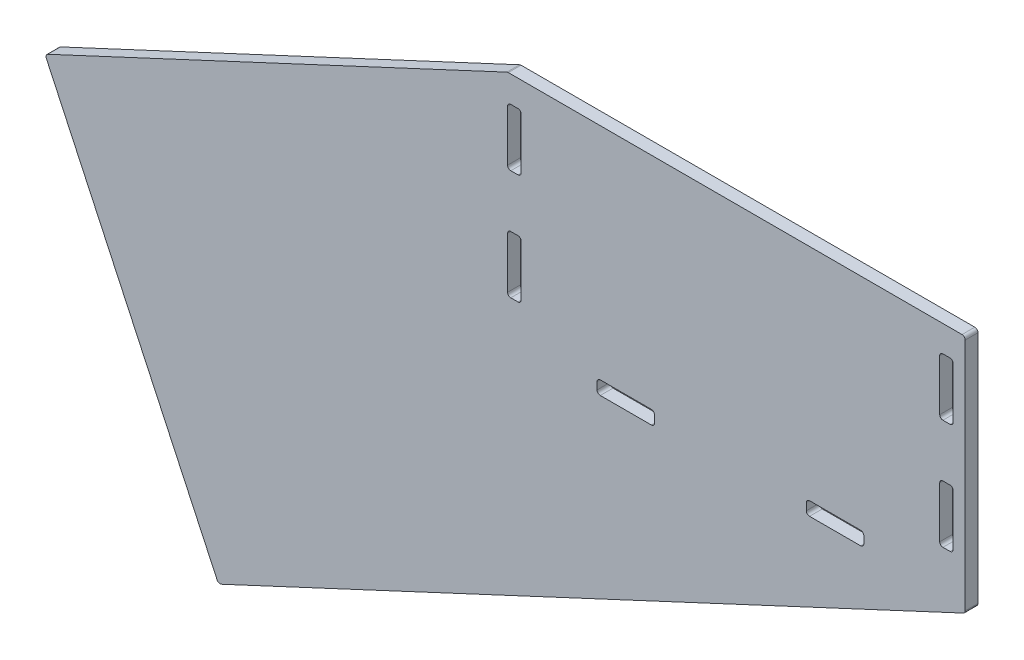
SolidWorks part; units mm, degrees
material "PE High Density"
ref_plane "Front Plane" through (0, 0, 0) normal (0, 0, 1) x (1, 0, 0)
ref_plane "Top Plane" through (0, 0, 0) normal (0, 1, 0) x (1, 0, 0)
ref_plane "Right Plane" through (0, 0, 0) normal (1, 0, 0) x (0, 0, -1)
sketch "Sketch1" plane through (0, 0, 0) normal (0, 0, 1) x (1, 0, 0)
  line L0 (-208.28, 0) -> (208.28, 0)
  line L1 (208.28, 0) -> (208.28, -219.075)
  line L2 (208.28, -219.075) -> (-208.28, -219.075)
  line L3 (-208.28, -219.075) -> (-208.28, 0)
  point P2 (0, 0)
  dimension "D1" = 219.075
  dimension "D2" = 416.56
extrude "Boss-Extrude1" add sketch "Sketch1" along normal mid plane 12.7
sketch "Sketch2" plane through (0, 0, 0) normal (0, 0, 1) x (1, 0, 0)
  line L0 (-221.742, 0) -> (-682.1464, -214.6901)
  line L1 (-682.1464, -214.6901) -> (-509.4341, -585.0727)
  line L2 (-509.4341, -585.0727) -> (233.68, -238.5529)
  line L3 (233.68, -238.5529) -> (233.68, 0)
  line L4 (233.68, 0) -> (208.28, 0)
  line L5 (208.28, 0) -> (208.28, -26.1938)
  line L6 (208.28, -219.075) -> (132.715, -219.075)
  line L7 (-208.28, -219.075) -> (-208.28, -192.8813)
  line L8 (208.28, 0) -> (-208.28, 0) construction
  line L9 (208.28, -219.075) -> (208.28, -244.475) construction
  line L10 (208.28, -83.3438) -> (208.28, -135.7312)
  line L11 (208.28, -26.1938) -> (221.742, -26.1938)
  line L13 (208.28, -83.3438) -> (221.742, -83.3438)
  line L14 (221.742, -26.1938) -> (221.742, -83.3438)
  line L15 (208.28, -135.7312) -> (221.742, -135.7313)
  line L17 (208.28, -192.8813) -> (221.742, -192.8812)
  line L18 (221.742, -135.7313) -> (221.742, -192.8812)
  line L20 (132.715, -219.075) -> (132.715, -232.537)
  line L21 (132.715, -232.537) -> (75.565, -232.537)
  line L22 (75.565, -219.075) -> (75.565, -232.537)
  line L23 (75.565, -219.075) -> (-75.565, -219.075)
  line L24 (208.28, -192.8813) -> (208.28, -219.075)
  line L25 (0, -6.985) -> (0, 6.985) construction
  line L26 (-75.565, -219.075) -> (-75.565, -232.537)
  line L27 (-132.715, -232.537) -> (-75.565, -232.537)
  line L28 (-132.715, -219.075) -> (-132.715, -232.537)
  line L29 (-208.28, -192.8813) -> (-221.742, -192.8813)
  line L30 (-221.742, -135.7312) -> (-221.742, -192.8813)
  line L31 (-208.28, -135.7312) -> (-221.742, -135.7312)
  line L32 (-208.28, -83.3438) -> (-221.742, -83.3438)
  line L33 (-208.28, -26.1938) -> (-221.742, -26.1938)
  line L34 (-221.742, -26.1938) -> (-221.742, -83.3438)
  line L35 (-208.28, -26.1938) -> (-208.28, 0)
  line L36 (-208.28, -135.7312) -> (-208.28, -83.3438)
  line L37 (-132.715, -219.075) -> (-208.28, -219.075)
  line L38 (208.28, 0) -> (208.28, -54.7688) construction
  line L39 (208.28, -219.075) -> (208.28, 0) construction
  line L40 (208.28, -219.075) -> (132.715, -219.075) construction
  line L41 (-75.565, -219.075) -> (75.565, -219.075) construction
  line L42 (-208.28, -219.075) -> (-132.715, -219.075) construction
  line L43 (208.28, -219.075) -> (104.14, -219.075) construction
  line L44 (-75.565, -219.075) -> (75.565, -219.075) construction
  line L45 (-208.28, -219.075) -> (208.28, -219.075) construction
  line L46 (208.28, -54.7688) -> (208.28, -109.5375) construction
  line L47 (208.28, -109.5375) -> (208.28, -164.3063) construction
  line L48 (208.28, -164.3063) -> (208.28, -219.075) construction
  line L49 (104.14, -219.075) -> (0, -219.075) construction
  line L50 (0, -219.075) -> (-104.14, -219.075) construction
  line L51 (-104.14, -219.075) -> (-208.28, -219.075) construction
  line L52 (208.28, -244.475) -> (220.98, -244.475) construction
  line L53 (220.98, -244.475) -> (220.98, -219.075) construction
  line L54 (220.98, -219.075) -> (208.28, -219.075) construction
  line L55 (-208.28, 0) -> (-221.742, 0)
  point P46 (221.742, -54.7688)
  point P48 (221.742, -164.3063)
  point P53 (-104.14, -232.537)
  point P55 (104.14, -232.537)
  dimension "D2" = 25.4
  dimension "D3" = 65
  dimension "D4" = 13.462
  dimension "D6" = 57.15
  dimension "D5" = 13.462
  dimension "D7" = 25.4
  dimension "D8" = 12.7
  dimension "D1" = 508
extrude "Boss-Extrude2" add sketch "Sketch2" along normal mid plane 12.7
fillet "Fillet1" radius 3.175 29 edges at (75.565, -232.537, 0) (75.565, -219.075, 0) (132.715, -232.537, 0) (132.715, -219.075, 0) (-132.715, -232.537, 0) (-132.715, -219.075, 0) (-75.565, -232.537, 0) (-75.565, -219.075, 0) (-221.742, -192.8813, 0) (-221.742, -135.7312, 0) (-208.28, -135.7312, 0) (-208.28, -192.8813, 0) (-208.28, -83.3438, 0) (-221.742, -83.3438, 0) (-208.28, -26.1938, 0) (-221.742, -26.1938, 0) (208.28, -135.7312, 0) (221.742, -135.7313, 0) (208.28, -192.8813, 0) (221.742, -192.8812, 0) (221.742, -83.3438, 0) (208.28, -83.3438, 0) (221.742, -26.1938, 0) (208.28, -26.1938, 0) (233.68, -238.5529, 0) (233.68, 0, 0) (-221.742, 0, 0) (-509.4341, -585.0727, 0) (-682.1464, -214.6901, 0)
equation "\"D5@Sketch2\"=\"D4@Sketch2\""
